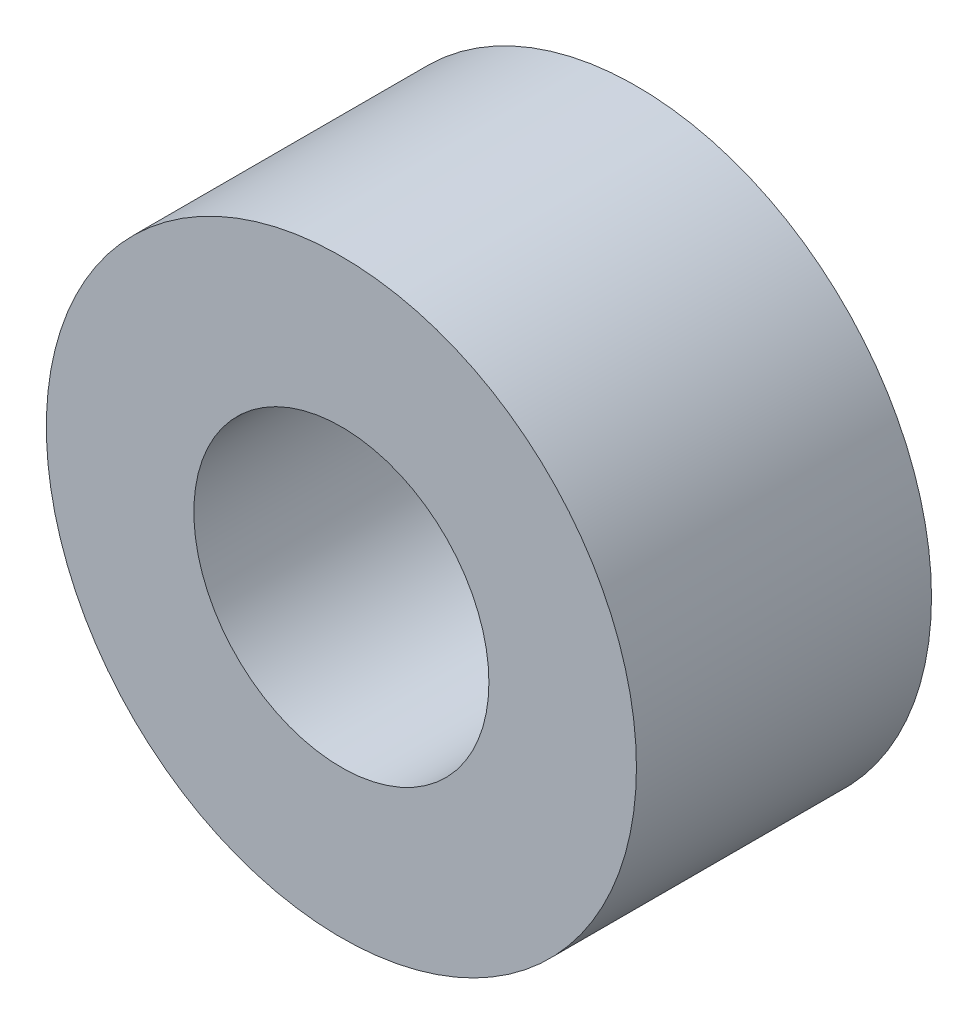
SolidWorks part; units mm, degrees
ref_plane "Front Plane" through (0, 0, 0) normal (0, 0, 1) x (1, 0, 0)
ref_plane "Top Plane" through (0, 0, 0) normal (0, 1, 0) x (1, 0, 0)
ref_plane "Right Plane" through (0, 0, 0) normal (1, 0, 0) x (0, 0, -1)
sketch "Sketch1" plane through (0, 0, 0) normal (0, 0, 1) x (1, 0, 0)
  circle A0 centre (0, 0) radius 1.5
  circle A1 centre (0, 0) radius 3
  dimension "D1" = 6
  dimension "D2" = 3
extrude "Boss-Extrude1" add sketch "Sketch1" along normal blind 3
